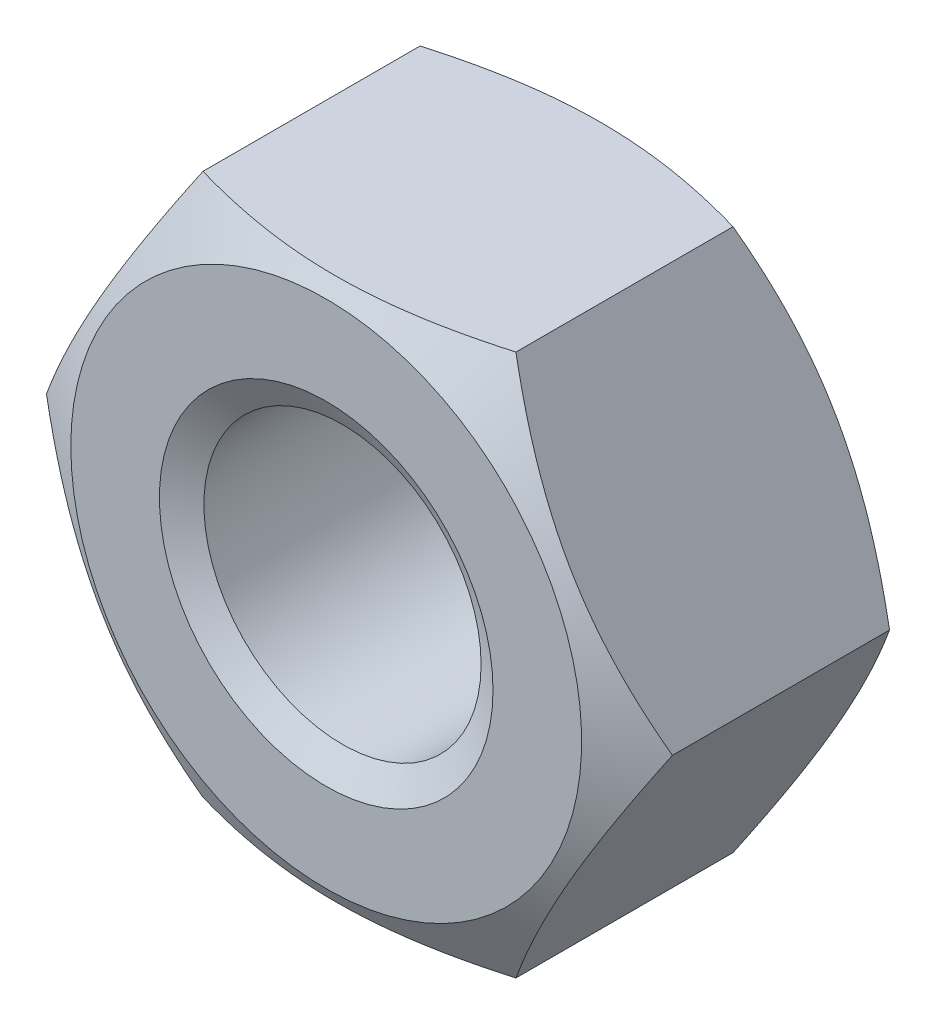
SolidWorks part; units mm, degrees
ref_plane "Front" through (0, 0, 0) normal (0, 0, 1) x (1, 0, 0)
ref_plane "Top" through (0, 0, 0) normal (0, 1, 0) x (1, 0, 0)
ref_plane "Right" through (0, 0, 0) normal (1, 0, 0) x (0, 0, -1)
sketch "Sketch1" plane through (0, 0, 0) normal (0, 0, 1) x (1, 0, 0)
  line L1 (7.5056, 0) -> (3.7528, 6.5)
  line L2 (3.7528, 6.5) -> (-3.7528, 6.5)
  line L3 (-3.7528, 6.5) -> (-7.5056, 0)
  line L4 (-7.5056, 0) -> (-3.7528, -6.5)
  line L5 (-3.7528, -6.5) -> (3.7528, -6.5)
  line L6 (3.7528, -6.5) -> (7.5056, 0)
  circle A0 centre (0, 0) radius 6.5 construction
  circle A1 centre (0, 0) radius 3.3235
  dimension "D" = 6.647
  dimension "s" = 13
extrude "BaseNut" add sketch "Sketch1" against normal blind 6.8
cosmetic thread "ThreadCosmetic1" [suppressed] parameters "D"=8
sketch "Sketch2" plane through (0, 0, 0) normal (0, 1, 0) x (1, 0, 0)
  line L0 (-7.5056, 6.8) -> (-6.125, 6.8)
  line L2 (-6.125, 6.8) -> (-7.5056, 6.0029)
  line L3 (-7.5056, 6.0029) -> (-7.5056, 6.8)
  line L4 (0, 3.3759) -> (0, -9.8171) construction
  line L6 (-9.7712, 3.4) -> (9.8853, 3.4) construction
  line L7 (-7.5056, 0.7971) -> (-7.5056, 0)
  line L8 (-6.125, 0) -> (-7.5056, 0.7971)
  line L9 (-7.5056, 0) -> (-6.125, 0)
  dimension "D1" = 30
  dimension "dw" = 12.25
  dimension "D2" = 3.4
revolve "Double-Chamfer" cut sketch "Sketch2" angle 360 about L4
chamfer "EndChamfer" distance 0.6765 angle 30 2 edges at (3.3235, 0, -6.8) (3.3235, 0, 0)
sketch "Sketch3" plane through (0, 0, 0) normal (0, 1, 0) x (1, 0, 0)
  line L0 (-3.9094, 6.1235) -> (-3.3235, 5.7853)
  line L1 (-3.3235, 5.7853) -> (-2.647, 5.7853)
  line L2 (-2.647, 5.7853) -> (-2.647, 6.4618)
  line L3 (-2.647, 6.4618) -> (-3.3235, 6.4618)
  line L4 (-3.3235, 6.4618) -> (-3.9094, 6.1235)
  line L5 (0, 7.4383) -> (0, 16.8806) construction
  dimension "D1" = 0.6765
  dimension "D2" = 6.647
revolve "Cut-Revolve10" [suppressed] cut sketch "Sketch3" angle 360 about L5
pattern_linear "LPattern10" [suppressed] count 8 spacing 0.8118 along (0, 0, -1)
equation "\"dw@Sketch2\" = \"s@Sketch1\"-0.75"
equation "\"D2@Sketch2\" = \"m@BaseNut\" / 2"
equation "\"D2@Sketch3\" = \"D@Sketch1\""
equation "\"D1@Sketch3\" =  (\"D@ThreadCosmetic1\"   - \"D@Sketch1\")  / 2"
equation "\"D3@LPattern10\" = \"D1@Sketch3\" * 1.2"
equation "\"D1@LPattern10\" = \"m@BaseNut\"/\"D3@LPattern10\""
